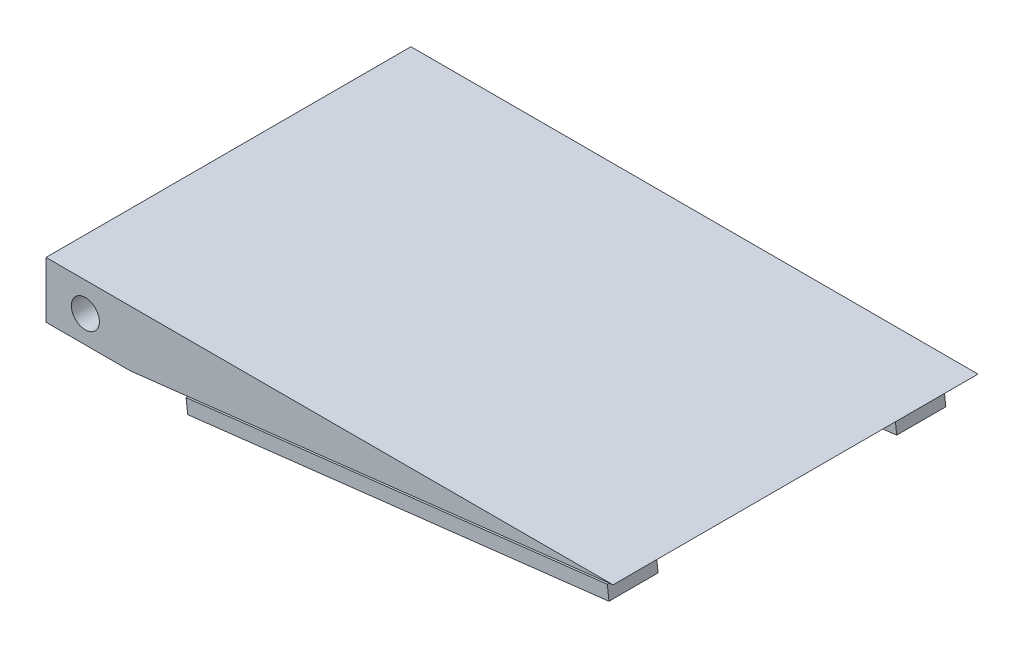
SolidWorks part; units mm, degrees
ref_plane "Front Plane" through (0, 0, 0) normal (0, 0, 1) x (1, 0, 0)
ref_plane "Top Plane" through (0, 0, 0) normal (0, 1, 0) x (1, 0, 0)
ref_plane "Right Plane" through (0, 0, 0) normal (1, 0, 0) x (0, 0, -1)
sketch "Sketch1" plane through (0, 0, 0) normal (0, 1, 0) x (1, 0, 0)
  line L1 (-227.828, 166.6055) -> (285.252, 166.6055)
  line L2 (-227.828, 166.6055) -> (-227.828, -163.5945)
  line L3 (-227.828, -163.5945) -> (285.252, -163.5945)
  line L4 (285.252, 166.6055) -> (285.252, -163.5945)
  dimension "D1" = 330.2
  dimension "D2" = 513.08
extrude "Boss-Extrude1" add sketch "Sketch1" along normal blind 50.8
sketch "Sketch2" plane through (0, 0, 163.5945) normal (0, 0, 1) x (1, 0, 0)
  line L0 (-151.628, 0) -> (285.252, 50.8)
  line L1 (-227.828, 0) -> (285.252, 0) construction
  line L2 (285.252, 50.8) -> (285.252, 0)
  line L3 (285.252, 0) -> (-151.628, 0)
  line L4 (-227.828, 50.8) -> (-227.828, 0) construction
  circle A0 centre (-192.2095, 24.5139) radius 12.7
  dimension "D1" = 76.2
extrude "Cut-Extrude1" cut sketch "Sketch2" against normal through all
sketch "Sketch3" plane through (-2.0228, 17.396, 0) normal (0.1155, -0.9933, 0) x (0.9933, 0.1155, 0)
  line L0 (289.2104, -166.6055) -> (-150.6132, -166.6055) construction
  line L1 (-113.9906, -122.1555) -> (268.9765, -122.1555)
  line L2 (-113.9906, -122.1555) -> (-113.9906, -141.2055)
  line L3 (-113.9906, -141.2055) -> (268.9765, -141.2055)
  line L4 (268.9765, -122.1555) -> (268.9765, -141.2055)
  dimension "D1" = 25.4
  dimension "D2" = 19.05
extrude "Boss-Extrude2" add sketch "Sketch3" along normal blind 12.7
sketch "Sketch4" plane through (-0.5559, 4.7809, 0) normal (0.1155, -0.9933, 0) x (0.9933, 0.1155, 0)
  line L0 (-113.9906, -141.2055) -> (268.9765, -141.2055) construction
  line L1 (-113.9906, -109.4555) -> (269.7315, -109.4555)
  line L2 (-113.9906, -109.4555) -> (-113.9906, -153.9055)
  line L3 (-113.9906, -153.9055) -> (269.7315, -153.9055)
  line L4 (269.7315, -109.4555) -> (269.7315, -153.9055)
  line L5 (268.9765, -122.1555) -> (-113.9906, -122.1555) construction
  dimension "D1" = 12.7
  dimension "D2" = 12.7
extrude "Boss-Extrude3" add sketch "Sketch4" along normal blind 12.7
ref_plane "Plane1" through (0, 0, -1.5055) normal (0, 0, 1) x (1, 0, 0)
mirror "Mirror1" about plane through (0, 0, -1.5055) normal (0, 0, 1) of "Boss-Extrude3", "Boss-Extrude2"
